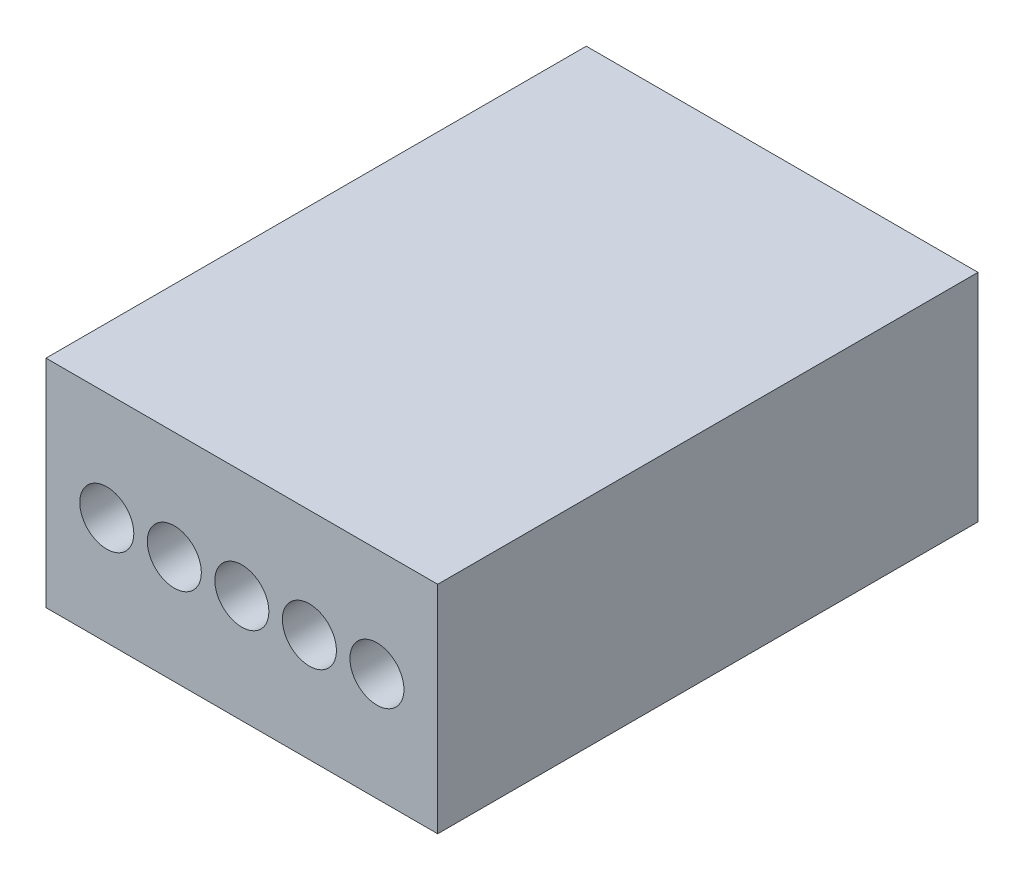
SolidWorks part; units mm, degrees
ref_plane "Front Plane" through (0, 0, 0) normal (0, 0, 1) x (1, 0, 0)
ref_plane "Top Plane" through (0, 0, 0) normal (0, 1, 0) x (1, 0, 0)
ref_plane "Right Plane" through (0, 0, 0) normal (1, 0, 0) x (0, 0, -1)
sketch "Sketch2" plane through (0, 0, 0) normal (0, 0, 1) x (1, 0, 0)
  line L1 (0, 0) -> (7.25, 0)
  line L2 (0, 0) -> (0, 4)
  line L3 (0, 4) -> (7.25, 4)
  line L4 (7.25, 0) -> (7.25, 4)
  dimension "D1" = 7.25
  dimension "D2" = 4
extrude "Boss-Extrude1" add sketch "Sketch2" along normal blind 10
sketch "Sketch3" plane through (0, 0, 10) normal (0, 0, 1) x (1, 0, 0)
  line L0 (0, 2) -> (7.25, 2) construction
  line L1 (0, 4) -> (0, 0) construction
  line L2 (7.25, 0) -> (7.25, 4) construction
  line L3 (0, 2) -> (7.25, 2) construction
  line L4 (7.25, 4) -> (0, 4) construction
  line L5 (0, 0) -> (7.25, 0) construction
  line L6 (1.125, 4) -> (1.125, 0) construction
  circle A0 centre (1.125, 2) radius 0.5
  circle A1 centre (2.375, 2) radius 0.5
  circle A2 centre (3.625, 2) radius 0.5
  circle A3 centre (4.875, 2) radius 0.5
  circle A4 centre (6.125, 2) radius 0.5
  circle A21 centre (24.875, 2) radius 0.5 [skipped]
  circle A22 centre (23.625, 2) radius 0.5 [skipped]
  circle A23 centre (22.375, 2) radius 0.5 [skipped]
  circle A24 centre (21.125, 2) radius 0.5 [skipped]
  circle A25 centre (19.875, 2) radius 0.5 [skipped]
  circle A26 centre (18.625, 2) radius 0.5 [skipped]
  circle A27 centre (17.375, 2) radius 0.5 [skipped]
  circle A28 centre (16.125, 2) radius 0.5 [skipped]
  circle A29 centre (14.875, 2) radius 0.5 [skipped]
  circle A30 centre (13.625, 2) radius 0.5 [skipped]
  circle A31 centre (12.375, 2) radius 0.5 [skipped]
  circle A32 centre (11.125, 2) radius 0.5 [skipped]
  circle A33 centre (9.875, 2) radius 0.5 [skipped]
  circle A34 centre (7.375, 2) radius 0.5 [skipped]
  circle A35 centre (8.625, 2) radius 0.5 [skipped]
  dimension "D1" = 1
  dimension "D2" = 2
  dimension "D3" = 1.125
  dimension "D5" = 1.25
  dimension "D4" = 20
extrude "Cut-Extrude1" cut sketch "Sketch3" against normal blind 5
sketch "Sketch4" plane through (0, 0, 10) normal (0, 0, 1) x (1, 0, 0)
  point P0 (1.125, 2)
  point P1 (2.375, 2)
  point P3 (3.625, 2)
  point P5 (4.875, 2)
  point P7 (6.125, 2)
  point P13 (0, 0)
  point P15 (0, 0)
  point P17 (0, 0)
  point P27 (0, 0)
  point P37 (0, 0)
